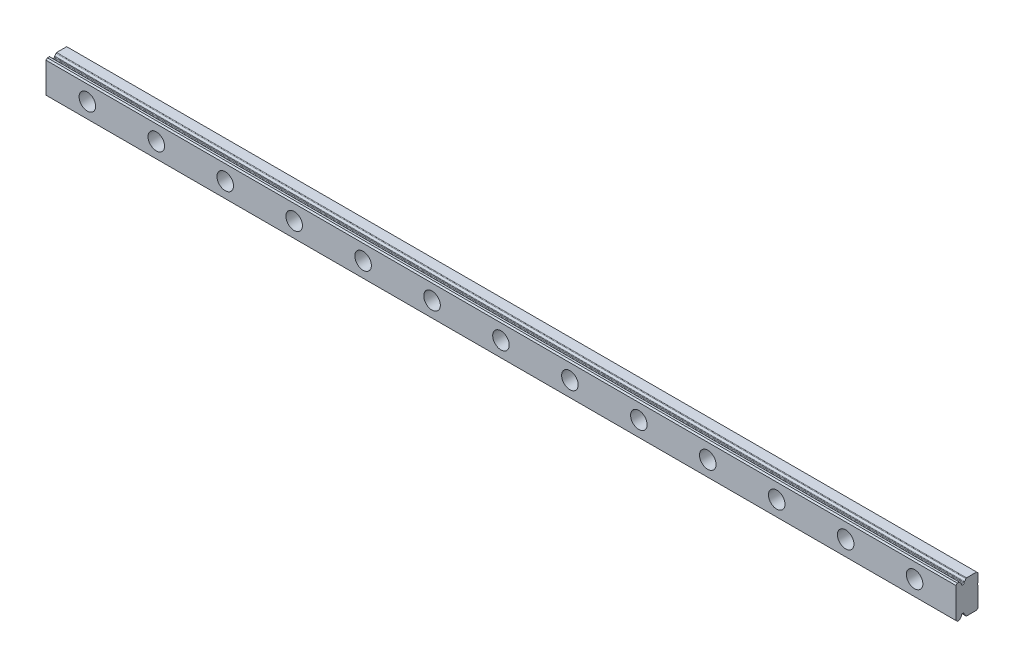
SolidWorks part; units mm, degrees
ref_plane "Front Plane" through (0, 0, 0) normal (0, 0, 1) x (1, 0, 0)
ref_plane "Top Plane" through (0, 0, 0) normal (0, 1, 0) x (1, 0, 0)
ref_plane "Right Plane" through (0, 0, 0) normal (1, 0, 0) x (0, 0, -1)
ref_plane "Plane1" through (315, 0, 0) normal (1, 0, 0) x (0, 0, -1)
sketch "Sketch1" plane through (315, 0, 0) normal (1, 0, 0) x (0, 0, -1)
  line L0 (-6.6457, -6) -> (-6.0865, -6)
  line L1 (-6.0865, -6) -> (-4.3219, -6)
  line L2 (-4.3219, -6) -> (-4.1421, -6)
  line L3 (-4.1421, -6) -> (-0.5, -6)
  line L4 (-0.5, -6) -> (0, -6)
  line L5 (0, -6) -> (0, -5.5)
  line L6 (0, -5.5) -> (0, 1.6)
  line L7 (0, 1.6) -> (0, 2.4)
  line L8 (0, 2.4) -> (0, 5.5)
  line L9 (0, 5.5) -> (0, 6)
  line L10 (0, 6) -> (-0.5, 6)
  line L11 (-0.5, 6) -> (-4.1421, 6)
  line L12 (-4.1421, 6) -> (-4.3219, 6)
  line L13 (-4.3219, 6) -> (-6.0865, 6)
  line L14 (-6.0865, 6) -> (-6.6457, 6)
  line L15 (-6.6457, 6) -> (-6.8254, 6)
  line L16 (-6.8254, 6) -> (-7.5, 6)
  line L17 (-7.5, 6) -> (-8, 5.5)
  line L18 (-8, 5.5) -> (-8, -5.5)
  line L19 (-8, -5.5) -> (-7.5, -6)
  line L20 (-7.5, -6) -> (-6.8254, -6)
  line L21 (-6.8254, -6) -> (-6.6457, -6)
extrude "Boss-Extrude1" add sketch "Sketch1" against normal blind 330
sketch "Sketch2" plane through (-15, 0, 0) normal (-1, 0, 0) x (0, 0, 1)
  line L0 (6.0865, -6) -> (6.0188, -5.2259)
  line L1 (6.0188, -5.2259) -> (6.0073, -5.0948)
  line L2 (6.0073, -5.0948) -> (5.9753, -4.7282)
  line L3 (5.9753, -4.7282) -> (5.9553, -4.5)
  line L4 (5.9553, -4.5) -> (5.7262, -4.5)
  line L5 (5.7262, -4.5) -> (5.2738, -4.5)
  line L6 (5.2738, -4.5) -> (5.0447, -4.5)
  line L7 (5.0447, -4.5) -> (5.0247, -4.7282)
  line L8 (5.0247, -4.7282) -> (4.9945, -5.0738)
  line L9 (4.9945, -5.0738) -> (4.9826, -5.2097)
  line L10 (4.3219, -6) -> (6.0865, -6)
  arc A0 (4.9826, -5.2097) -> (4.3219, -6) centre (5.4838, -6.3) ccw
extrude "Cut-Extrude1" cut sketch "Sketch2" against normal through all
sketch "Sketch3" plane through (-15, 0, 0) normal (-1, 0, 0) x (0, 0, 1)
  line L0 (0, 2.4) -> (0, 1.6)
  arc A0 (0, 1.6) -> (0, 2.4) centre (-0.3, 2) ccw
extrude "Cut-Extrude2" cut sketch "Sketch3" against normal through all
sketch "Sketch4" plane through (-15, 0, 0) normal (-1, 0, 0) x (0, 0, 1)
  line L0 (6.0073, 5.0948) -> (6.0188, 5.2259)
  line L1 (6.0188, 5.2259) -> (6.0865, 6)
  line L2 (6.0865, 6) -> (4.3219, 6)
  line L3 (4.9826, 5.2097) -> (4.9945, 5.0738)
  line L4 (4.9945, 5.0738) -> (5.0247, 4.7282)
  line L5 (5.0247, 4.7282) -> (5.0447, 4.5)
  line L6 (5.0447, 4.5) -> (5.2738, 4.5)
  line L7 (5.2738, 4.5) -> (5.7262, 4.5)
  line L8 (5.7262, 4.5) -> (5.9553, 4.5)
  line L9 (5.9553, 4.5) -> (5.9753, 4.7282)
  line L10 (5.9753, 4.7282) -> (6.0073, 5.0948)
  arc A0 (4.3219, 6) -> (4.9826, 5.2097) centre (5.4838, 6.3) ccw
extrude "Cut-Extrude3" cut sketch "Sketch4" against normal through all
sketch "Sketch5" plane through (-15, 0, 0) normal (-1, 0, 0) x (0, 0, 1)
  line L0 (6.0865, 6) -> (6.0188, 5.2259)
  line L1 (6.6457, 6) -> (6.0865, 6)
  arc A0 (6.0188, 5.2259) -> (6.6457, 6) centre (5.4838, 6.3) ccw
extrude "Cut-Extrude4" cut sketch "Sketch5" against normal through all
sketch "Sketch6" plane through (-15, 0, 0) normal (-1, 0, 0) x (0, 0, 1)
  line L0 (6.0865, -6) -> (6.6457, -6)
  line L1 (6.0188, -5.2259) -> (6.0865, -6)
  arc A0 (6.6457, -6) -> (6.0188, -5.2259) centre (5.4838, -6.3) ccw
extrude "Cut-Extrude5" cut sketch "Sketch6" against normal through all
hole_wizard "CBORE for M3 Hex Head Machine Screw1" positions "Sketch8" profile "Sketch7" counterbore size "M3" standard "ANSI Metric"
sketch "Sketch8" plane through (0, 0, 8) normal (0, 0, 1) x (1, 0, 0)
  point P0 (300, 0)
  point P1 (25, 0)
  point P2 (50, 0)
  point P3 (75, 0)
  point P4 (100, 0)
  point P5 (125, 0)
  point P6 (150, 0)
  point P7 (175, 0)
  point P8 (200, 0)
  point P9 (225, 0)
  point P10 (250, 0)
  point P11 (275, 0)
  point P12 (0, 0)
sketch "Sketch7" plane through (300, 0, 8) normal (1, 0, 0) x (0, -1, 0)
  line L0 (0, 0) -> (0, 8)
  line L1 (0, 8) -> (1.75, 8)
  line L3 (1.75, 8) -> (1.75, 4.5)
  line L4 (1.75, 4.5) -> (3, 4.5)
  line L5 (3, 4.5) -> (3, 0)
  line L7 (3, 0) -> (0, 0)
  line L11 (0, -6.35) -> (0, 107.95) construction
  dimension "Thru Hole Dia." = 3.5
  dimension "Thru Hole Depth" = 8
  dimension "C'Bore Dia." = 6
  dimension "C'Bore Depth" = 4.5
chamfer "Chamfer1" distance 0.5 angle 45 2 edges at (150, 6, 0) (150, -6, 0)
fillet "Fillet1" radius 0.25 12 edges at (150, 4.5, 5.9553) (150, 4.5, 5.0447) (150, 5.2097, 4.9826) (150, 6, 4.3219) (150, 6, 6.6457) (150, 5.2259, 6.0188) (150, -5.2259, 6.0188) (150, -6, 6.6457) (150, -6, 4.3219) (150, -5.2097, 4.9826) (150, -4.5, 5.0447) (150, -4.5, 5.9553)
